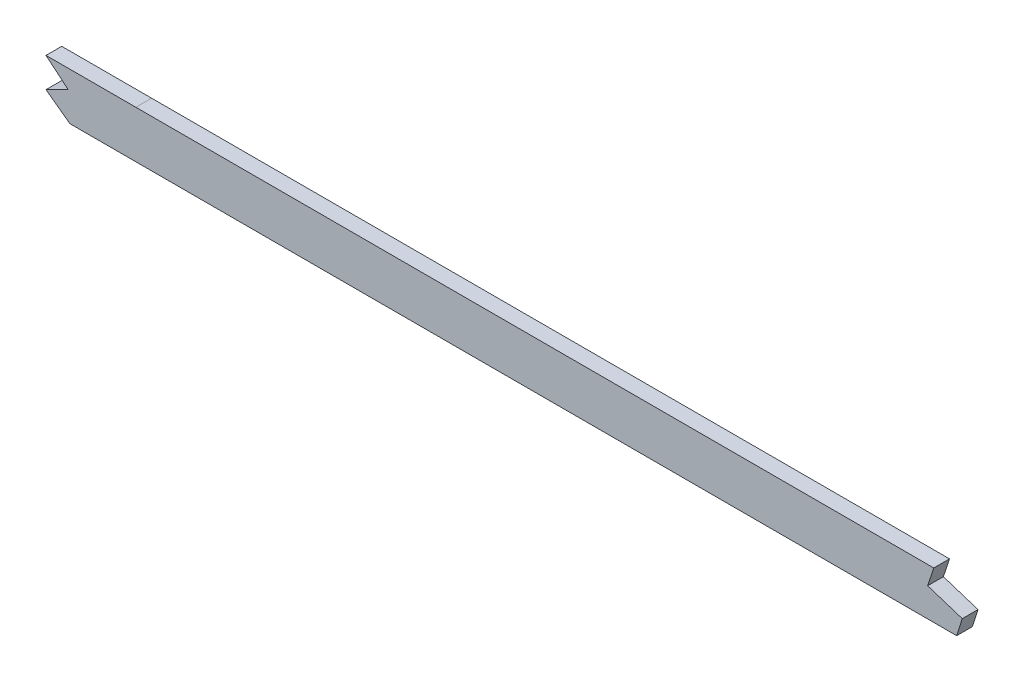
SolidWorks part; units mm, degrees
ref_plane "Front Plane" through (0, 0, 0) normal (0, 0, 1) x (1, 0, 0)
ref_plane "Top Plane" through (0, 0, 0) normal (0, 1, 0) x (1, 0, 0)
ref_plane "Right Plane" through (0, 0, 0) normal (1, 0, 0) x (0, 0, -1)
sketch "Sketch1" plane through (0, 0, 0) normal (0, 0, 1) x (1, 0, 0)
  line L0 (1046.2855, 53.4707) -> (499.61, 53.4707) construction
  line L1 (55, 0) -> (-55, 0) construction
  line L2 (1046.2855, -53.4707) -> (499.61, -53.4707)
  line L3 (1046.2855, -34.4207) -> (499.61, -34.4207)
  line L4 (99.06, -18.1493) -> (99.06, -37.7415)
  line L5 (2669.54, 9.5231) -> (2669.54, -9.569)
  spline S0 degree 5 poles (2699.7923, 7.5245) (2639.6368, 11.6572) (2579.4813, 15.4358) (2518.4981, 19.1485) (2436.3555, 23.2524) (2354.213, 26.6315) (2332.5703, 27.481) (2156.2686, 34.3778) (1979.9669, 41.6286) (1824.1143, 52.7713) (1636.9286, 53.5796) (1449.7429, 53.454) (1418.0067, 53.4707) (1324.8993, 53.4707) (1231.7919, 53.4707) (1170.4413, 53.4707) (1108.7841, 53.4707) (1047.1269, 53.4707) (1046.8464, 53.4707) (1046.5659, 53.4707) (1046.2855, 53.4707) knots 100.654805 100.654805 100.654805 100.654805 100.654805 100.654805 130.927897 130.927897 130.927897 141.337055 141.337055 141.337055 218.101815 218.101815 218.101815 233.772059 233.772059 233.772059 264.077723 264.077723 264.077723 264.216209 264.216209 264.216209 264.216209 264.216209 264.216209 weights 1 1 1 1 1 1 1 1 1 1 1 1 1 1 1 1 1 1 1 1 1 construction
  spline S1 degree 5 poles (499.61, 53.4707) (492.1368, 53.4707) (484.7543, 53.4707) (477.443, 53.4707) (448.5166, 53.4707) (419.5901, 53.4707) (398.3681, 53.4707) (355.6475, 53.4707) (312.927, 53.4707) (289.2351, 53.4703) (265.365, 53.4707) (241.4948, 53.4707) (241.4716, 53.4707) (241.4484, 53.4707) (241.4251, 53.4707) knots 19.90683 19.90683 19.90683 19.90683 19.90683 19.90683 23.637897 23.637897 23.637897 34.276546 34.276546 34.276546 46.401341 46.401341 46.401341 46.413154 46.413154 46.413154 46.413154 46.413154 46.413154 weights 1 1 1 1 1 1 1 1 1 1 1 1 1 1 1 construction
  spline S2 degree 5 poles (241.4251, 53.4707) (224.2869, 53.4707) (207.1495, 53.4673) (190.2039, 52.6866) (151.6561, 49.0319) (113.1083, 41.5037) (91.9499, 36.3426) (71.313, 30.9696) (50.6762, 24.7565) knots 0 0 0 0 0 0 8.713816 8.713816 8.713816 19.90683 19.90683 19.90683 19.90683 19.90683 19.90683 weights 1 1 1 1 1 1 1 1 1 construction
  spline S3 degree 5 poles (241.4251, -53.4707) (224.2869, -53.4707) (207.1495, -53.4673) (190.2039, -52.6866) (151.6561, -49.0319) (113.1083, -41.5037) (91.9499, -36.3426) (71.313, -30.9696) (50.6762, -24.7565) knots 0 0 0 0 0 0 8.713816 8.713816 8.713816 19.90683 19.90683 19.90683 19.90683 19.90683 19.90683 weights 1 1 1 1 1 1 1 1 1
  spline S4 degree 5 poles (499.61, -53.4707) (492.1368, -53.4707) (484.7543, -53.4707) (477.443, -53.4707) (448.5166, -53.4707) (419.5901, -53.4707) (398.3681, -53.4707) (355.6475, -53.4707) (312.927, -53.4707) (289.2351, -53.4703) (265.365, -53.4707) (241.4948, -53.4707) (241.4716, -53.4707) (241.4484, -53.4707) (241.4251, -53.4707) knots 19.90683 19.90683 19.90683 19.90683 19.90683 19.90683 23.637897 23.637897 23.637897 34.276546 34.276546 34.276546 46.401341 46.401341 46.401341 46.413154 46.413154 46.413154 46.413154 46.413154 46.413154 weights 1 1 1 1 1 1 1 1 1 1 1 1 1 1 1
  spline S5 degree 5 poles (2699.7923, -7.5245) (2639.6368, -11.6572) (2579.4813, -15.4358) (2518.4981, -19.1485) (2436.3555, -23.2524) (2354.213, -26.6315) (2332.5703, -27.481) (2156.2686, -34.3778) (1979.9669, -41.6286) (1824.1143, -52.7713) (1636.9286, -53.5796) (1449.7429, -53.454) (1418.0067, -53.4707) (1324.8993, -53.4707) (1231.7919, -53.4707) (1170.4413, -53.4707) (1108.7841, -53.4707) (1047.1269, -53.4707) (1046.8464, -53.4707) (1046.5659, -53.4707) (1046.2855, -53.4707) knots 100.654805 100.654805 100.654805 100.654805 100.654805 100.654805 130.927897 130.927897 130.927897 141.337055 141.337055 141.337055 218.101815 218.101815 218.101815 233.772059 233.772059 233.772059 264.077723 264.077723 264.077723 264.216209 264.216209 264.216209 264.216209 264.216209 264.216209 weights 1 1 1 1 1 1 1 1 1 1 1 1 1 1 1 1 1 1 1 1 1
  spline S6 degree 1 poles (2698.4867, 11.4807) (1046.2855, -34.4207) knots 0 0 1 1 construction
  spline S7 degree 1 poles (499.61, -34.4207) (241.4252, -34.4207) knots 0 0 1 1 construction
  spline S8 degree 1 poles (241.4252, -34.4207) (56.168, -6.5153) knots 0 0 1 1 construction
  spline S9 degree 3 poles (2698.4867, 11.4807) (2691.2474, 10.9833) (2679.1952, 10.1655) (2662.2765, 9.0388) (2635.6663, 7.2925) (2596.8577, 4.8261) (2545.7297, 1.7583) (2494.4053, -1.0986) (2451.533, -3.2666) (2417.1983, -4.8671) (2391.4571, -6.0036) (2365.6347, -7.0869) (2339.5463, -8.1377) (2313.4661, -9.1651) (2287.6124, -10.1795) (2261.7633, -11.201) (2227.2853, -12.5838) (2184.1756, -14.3661) (2132.4291, -16.6074) (2063.4255, -19.7089) (1977.1749, -23.7005) (1873.7325, -28.1494) (1770.3746, -31.6575) (1667.0857, -33.7931) (1581.0111, -34.3832) (1512.074, -34.4278) (1443.0615, -34.4095) (1356.8009, -34.4244) (1218.7946, -34.4185) (1115.289, -34.4207) (1046.2855, -34.4207) knots 100.654805 100.654805 100.654805 100.654805 102.842388 104.300777 105.766098 110.877392 115.988686 121.09998 126.211274 128.766921 131.322568 133.878215 136.433862 138.989509 141.545156 144.100803 146.656449 151.767743 156.879037 161.990331 172.212919 182.435507 192.658094 202.880682 213.10327 218.214564 223.325858 233.548445 243.771033 264.216209 264.216209 264.216209 264.216209
  spline S10 degree 3 poles (499.61, -34.4207) (488.6147, -34.4207) (472.2364, -34.4207) (449.9402, -34.4207) (427.7713, -34.4207) (405.8747, -34.4207) (384.5849, -34.4207) (368.9002, -34.4207) (353.3766, -34.4207) (332.6085, -34.4207) (306.2878, -34.4206) (274.0235, -34.4205) (252.271, -34.4207) (241.4252, -34.4207) knots 19.90683 19.90683 19.90683 19.90683 23.22012 24.876765 26.533411 29.846701 31.503346 33.159992 34.816637 36.473282 39.786573 43.099863 46.413154 46.413154 46.413154 46.413154
  spline S11 degree 3 poles (241.4252, -34.4207) (239.3949, -34.4207) (235.3223, -34.4205) (227.2744, -34.3987) (217.3194, -34.2975) (205.5307, -33.9764) (189.9633, -33.2126) (170.697, -31.5435) (147.5333, -28.3144) (125.4828, -24.2021) (107.4399, -20.1965) (92.2061, -16.4882) (75.9505, -12.2555) (63.6202, -8.7589) (56.168, -6.5153) knots 0 0 0 0 0.622088 1.244177 2.488354 3.732531 4.976707 7.465061 9.953415 12.441768 14.558235 15.802412 17.418476 19.90683 19.90683 19.90683 19.90683
  point P2 (0, 0)
  dimension "D1" = 50.6762
  dimension "D3" = 99.06
  dimension "D4" = 2669.54
  dimension "D2" = 19.05
extrude "Boss-Extrude1" add sketch "Sketch1" along normal mid plane 6.35 contours S10 S11 L4 S3 S4 L2 S5 L5 S9 L3
sketch "Sketch2" plane through (0, 0, 3.175) normal (0, 0, 1) x (1, 0, 0)
  line L0 (2187.01, -14.2633) -> (2312.9875, -14.2633)
  line L1 (2312.9875, -14.2633) -> (2312.9875, -9.1833)
  spline S0 degree 3 poles (689.0175, 232.3189) (4033.8285, 148.9311) (3356.6623, 54.6077) (2635.6663, 7.2925) (2596.8577, 4.8261) (2545.7297, 1.7583) (2494.4053, -1.0986) (2451.533, -3.2666) (2417.1983, -4.8671) (2391.4571, -6.0036) (2365.6347, -7.0869) (2339.5463, -8.1377) (2313.4661, -9.1651) (2287.6124, -10.1795) (2261.7633, -11.201) (2227.2853, -12.5838) (2184.1756, -14.3661) (2132.4291, -16.6074) (2063.4255, -19.7089) (1977.1749, -23.7005) (1873.7325, -28.1494) (1770.3746, -31.6575) (1667.0857, -33.7931) (1581.0111, -34.3832) (1512.074, -34.4278) (1443.0615, -34.4095) (1356.8009, -34.4244) (551.9641, -34.3896) (-218.4198, -34.7282) (-953.6342, -29.9632) knots -106.828462 -106.828462 -106.828462 -106.828462 104.300777 105.766098 110.877392 115.988686 121.09998 126.211274 128.766921 131.322568 133.878215 136.433862 138.989509 141.545156 144.100803 146.656449 151.767743 156.879037 161.990331 172.212919 182.435507 192.658094 202.880682 213.10327 218.214564 223.325858 233.548445 243.771033 461.793666 461.793666 461.793666 461.793666 only from (2669.54, 9.5231) to (1046.2855, -34.4207) construction
  spline S1 degree 3 poles (2669.54, 9.5231) (2667.1265, 9.3624) (2659.8616, 8.8803) (2635.6663, 7.2925) (2596.8577, 4.8261) (2545.7297, 1.7583) (2494.4053, -1.0986) (2451.533, -3.2666) (2417.1983, -4.8671) (2391.4571, -6.0036) (2365.6347, -7.0869) (2339.5463, -8.1377) (2313.4661, -9.1651) (2287.6124, -10.1795) (2261.7633, -11.201) (2227.2853, -12.5838) (2184.1756, -14.3661) (2132.4291, -16.6074) (2063.4255, -19.7089) (1977.1749, -23.7005) (1873.7325, -28.1494) (1770.3746, -31.6575) (1667.0857, -33.7931) (1581.0111, -34.3832) (1512.074, -34.4278) (1443.0615, -34.4095) (1356.8009, -34.4244) (1218.7946, -34.4185) (1115.289, -34.4207) (1046.2855, -34.4207) knots 103.571583 103.571583 103.571583 103.571583 104.300777 105.766098 110.877392 115.988686 121.09998 126.211274 128.766921 131.322568 133.878215 136.433862 138.989509 141.545156 144.100803 146.656449 151.767743 156.879037 161.990331 172.212919 182.435507 192.658094 202.880682 213.10327 218.214564 223.325858 233.548445 243.771033 264.216209 264.216209 264.216209 264.216209
  point P2 (0, 0)
  spline M9 degree 3 poles (2698.4867, 11.4807) (2691.2474, 10.9833) (2679.1952, 10.1655) (2662.2765, 9.0388) (2635.6663, 7.2925) (2596.8577, 4.8261) (2545.7297, 1.7583) (2494.4053, -1.0986) (2451.533, -3.2666) (2417.1983, -4.8671) (2391.4571, -6.0036) (2365.6347, -7.0869) (2339.5463, -8.1377) (2313.4661, -9.1651) (2287.6124, -10.1795) (2261.7633, -11.201) (2227.2853, -12.5838) (2184.1756, -14.3661) (2132.4291, -16.6074) (2063.4255, -19.7089) (1977.1749, -23.7005) (1873.7325, -28.1494) (1770.3746, -31.6575) (1667.0857, -33.7931) (1581.0111, -34.3832) (1512.074, -34.4278) (1443.0615, -34.4095) (1356.8009, -34.4244) (1218.7946, -34.4185) (1115.289, -34.4207) (1046.2855, -34.4207) knots 100.654805 100.654805 100.654805 100.654805 102.842388 104.300777 105.766098 110.877392 115.988686 121.09998 126.211274 128.766921 131.322568 133.878215 136.433862 138.989509 141.545156 144.100803 146.656449 151.767743 156.879037 161.990331 172.212919 182.435507 192.658094 202.880682 213.10327 218.214564 223.325858 233.548445 243.771033 264.216209 264.216209 264.216209 264.216209 only from (2669.54, 9.5231) to (1046.2855, -34.4207)
  dimension "D1" = 2312.9875
  dimension "D2" = 5.08
extrude "Cut-Extrude1" cut sketch "Sketch2" against normal through all contours L0 L1 M9
fillet "Fillet1" radius 2.54 6 edges at (2669.54, -9.569, 0) (2669.54, 9.5231, 0) (99.06, -37.7415, 0) (99.06, -18.1493, 0) (2312.9875, -14.2633, 0)
sketch "Sketch3" plane through (0, 0, 3.175) normal (0, 0, 1) x (1, 0, 0)
  line L0 (463.3586, -34.4207) -> (472.2717, -41.8744)
  line L3 (1046.2855, -34.4207) -> (499.61, -34.4207) construction
  line L4 (1046.2855, -53.4707) -> (499.61, -53.4707) construction
  line L10 (472.2717, -41.8744) -> (463.3586, -46.3842)
  line L11 (463.3586, -46.3842) -> (472.9974, -53.4707)
  line L12 (821.5189, -34.4207) -> (819.0473, -41.8744)
  line L13 (819.0473, -41.8744) -> (833.0048, -46.3842)
  line L14 (833.0048, -46.3842) -> (830.7563, -53.4707)
  line L28 (463.3586, -34.4207) -> (463.3586, 108.2637)
  line L29 (463.3586, 108.2637) -> (36.2374, 16.7013)
  line L30 (36.2374, 16.7013) -> (65.9601, -189.8713)
  line L31 (65.9601, -189.8713) -> (472.9974, -53.4707)
  line L32 (821.5189, -34.4207) -> (821.5189, 129.6915)
  line L33 (821.5189, 129.6915) -> (2725.4905, 129.6915)
  line L34 (2725.4905, 129.6915) -> (2725.4905, -272.2237)
  line L35 (2725.4905, -272.2237) -> (830.7563, -93.6712)
  line L36 (830.7563, -93.6712) -> (830.7563, -53.4707)
  spline S0 degree 3 poles (499.61, -34.4207) (488.6147, -34.4207) (472.2364, -34.4207) (449.9402, -34.4207) (427.7713, -34.4207) (405.8747, -34.4207) (384.5849, -34.4207) (368.9002, -34.4207) (353.3766, -34.4207) (332.6085, -34.4207) (306.2878, -34.4206) (274.0235, -34.4205) (252.271, -34.4207) (241.4252, -34.4207) knots 19.90683 19.90683 19.90683 19.90683 23.22012 24.876765 26.533411 29.846701 31.503346 33.159992 34.816637 36.473282 39.786573 43.099863 46.413154 46.413154 46.413154 46.413154 construction
  spline S1 degree 5 poles (499.61, -53.4707) (492.1368, -53.4707) (484.7543, -53.4707) (477.443, -53.4707) (448.5166, -53.4707) (419.5901, -53.4707) (398.3681, -53.4707) (355.6475, -53.4707) (312.927, -53.4707) (289.2351, -53.4703) (265.365, -53.4707) (241.4948, -53.4707) (241.4716, -53.4707) (241.4484, -53.4707) (241.4251, -53.4707) knots 19.90683 19.90683 19.90683 19.90683 19.90683 19.90683 23.637897 23.637897 23.637897 34.276546 34.276546 34.276546 46.401341 46.401341 46.401341 46.413154 46.413154 46.413154 46.413154 46.413154 46.413154 weights 1 1 1 1 1 1 1 1 1 1 1 1 1 1 1 construction
extrude "Cut-Extrude2" cut sketch "Sketch3" against normal blind 7.62
